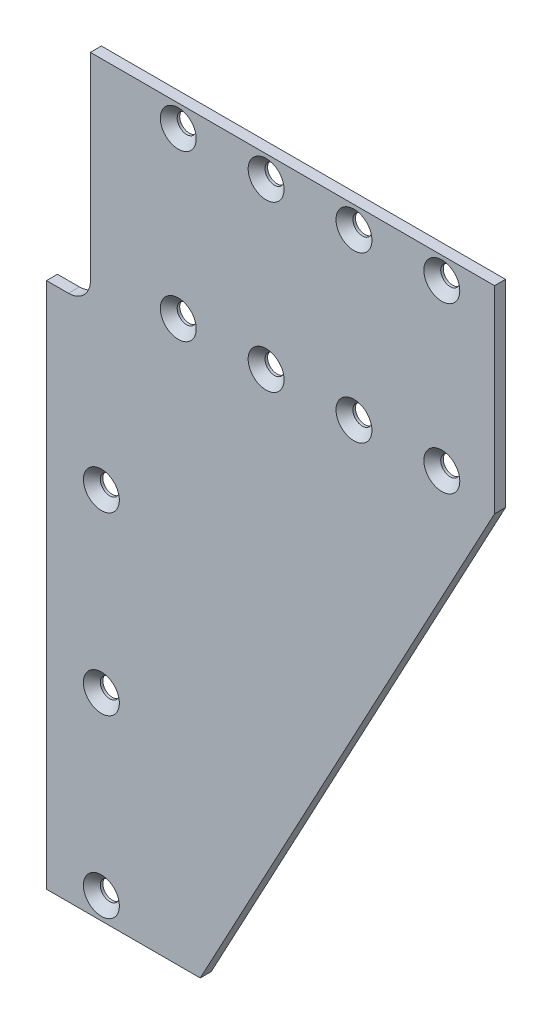
SolidWorks part; units mm, degrees
material "ASTM A36 Steel"
ref_plane "Front Plane" through (0, 0, 0) normal (0, 0, 1) x (1, 0, 0)
ref_plane "Top Plane" through (0, 0, 0) normal (0, 1, 0) x (1, 0, 0)
ref_plane "Right Plane" through (0, 0, 0) normal (1, 0, 0) x (0, 0, -1)
sketch "Sketch1" plane through (0, 0, 0) normal (0, 0, 1) x (1, 0, 0)
  line L0 (0, 0) -> (0, 152.4)
  line L7 (0, 0) -> (0, 282.9449) construction
  line L8 (6.35, 152.4) -> (0, 152.4)
  line L9 (12.7, 215.9) -> (12.7, 158.75)
  line L10 (12.7, 215.9) -> (129.54, 215.9)
  line L11 (129.54, 215.9) -> (129.54, 158.75)
  line L12 (129.54, 158.75) -> (44.45, 0)
  line L13 (44.45, 0) -> (0, 0)
  arc A1 (12.7, 158.75) -> (6.35, 152.4) centre (6.35, 158.75) cw
  point P11 (-12.7, 152.4)
  dimension "D7" = 6.35
  dimension "D1" = 152.4
  dimension "D2" = 215.9
  dimension "D3" = 44.45
  dimension "D4" = 129.54
  dimension "D5" = 12.7
  dimension "D6" = 57.15
extrude "Boss-Extrude1" add sketch "Sketch1" against normal blind 3.175
sketch "Sketch2" plane through (0, 0, 0) normal (0, 0, 1) x (1, 0, 0)
  line L0 (129.54, 215.9) -> (12.7, 215.9) construction
  line L3 (12.7, 215.9) -> (12.7, 158.75) construction
  line L8 (38.1, 209.55) -> (114.3, 209.55) construction
  line L9 (38.1, 161.925) -> (114.3, 161.925) construction
  line L10 (15.875, 57.15) -> (15.875, 6.35) construction
  line L11 (0, 0) -> (44.45, 0) construction
  line L12 (15.875, 57.15) -> (15.875, 107.95) construction
  line L13 (0, 152.4) -> (0, 0) construction
  dimension "D2" = 6.35
  dimension "D3" = 76.2
  dimension "D4" = 25.4
  dimension "D5" = 47.625
  dimension "D9" = 6.35
  dimension "D10" = 50.8
  dimension "D11" = 50.8
  dimension "D12" = 15.875
hole_wizard "CSK for #0 Flat Head Machine Screw (100)1" positions "3DSketch1" profile "Sketch3" countersink size "#0" standard "ANSI Inch" end condition through all
sketch3d "3DSketch1"
  point P12 (38.1, 209.55, 0)
  point P15 (38.1, 161.925, 0)
sketch "Sketch3" plane through (38.1, 209.55, 0) normal (1, 0, 0) x (0, -1, 0)
  line L0 (0, 0) -> (0, 3.175)
  line L1 (0, 3.175) -> (2.7559, 3.175)
  line L2 (2.7559, 3.175) -> (2.7559, 2.4384)
  line L3 (2.7559, 2.4384) -> (5.1943, 0)
  line L5 (5.1943, 0) -> (0, 0)
  line L6 (-2.7559, 2.4384) -> (-5.1943, 0) construction
  line L11 (0, -6.35) -> (0, 107.95) construction
  dimension "Thru Hole Dia." = 5.5118
  dimension "Thru Hole Depth" = 3.175
  dimension "Near C'Sink Dia." = 10.3886
  dimension "Near C'Sink Angle" = 90
pattern_linear "LPattern1" count 4 spacing 25.4 along (1, 0, 0) of "CSK for #0 Flat Head Machine Screw (100)1"
hole_wizard "CSK for #0 Flat Head Machine Screw (100)2" positions "3DSketch2" profile "Sketch4" countersink size "#0" standard "ANSI Inch" end condition through all
sketch3d "3DSketch2"
  point P6 (15.875, 107.95, 0)
sketch "Sketch4" plane through (15.875, 107.95, 0) normal (1, 0, 0) x (0, -1, 0)
  line L0 (0, 0) -> (0, 3.175)
  line L1 (0, 3.175) -> (2.7559, 3.175)
  line L2 (2.7559, 3.175) -> (2.7559, 2.4384)
  line L3 (2.7559, 2.4384) -> (5.1943, 0)
  line L5 (5.1943, 0) -> (0, 0)
  line L6 (-2.7559, 2.4384) -> (-5.1943, 0) construction
  line L11 (0, -6.35) -> (0, 107.95) construction
  dimension "Thru Hole Dia." = 5.5118
  dimension "Thru Hole Depth" = 3.175
  dimension "Near C'Sink Dia." = 10.3886
  dimension "Near C'Sink Angle" = 90
pattern_linear "LPattern2" count 3 spacing 50.8 along (0, -1, 0) of "CSK for #0 Flat Head Machine Screw (100)2"
